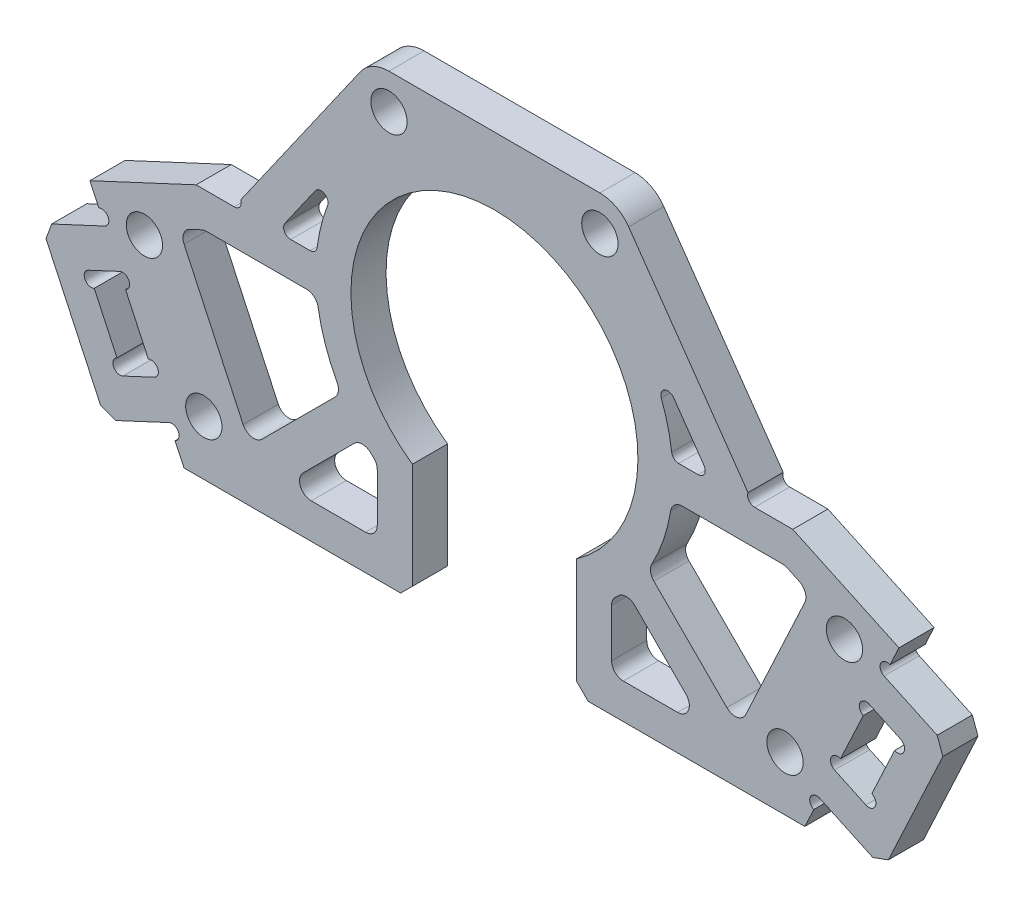
SolidWorks part; units mm, degrees
ref_plane "前视基准面" through (0, 0, 0) normal (0, 0, 1) x (1, 0, 0)
ref_plane "上视基准面" through (0, 0, 0) normal (0, 1, 0) x (1, 0, 0)
ref_plane "右视基准面" through (0, 0, 0) normal (1, 0, 0) x (0, 0, -1)
sketch "草图1" plane through (0, 0, 0) normal (0, 0, 1) x (1, 0, 0)
  line L0 (-34.5264, 8.6099) -> (-26.4967, -8.6099)
  line L1 (-29.455, -2.2658) -> (0, 11.4693) construction
  line L2 (0, -8.6099) -> (0, 8.6099) construction
  line L3 (-34.5264, 8.6099) -> (-25.4633, 12.8361)
  line L4 (-26.4967, -8.6099) -> (26.4967, -8.6099)
  line L5 (34.5264, 8.6099) -> (26.4967, -8.6099)
  line L6 (34.5264, 8.6099) -> (25.4633, 12.8361)
  line L7 (-25.4633, 12.8361) -> (25.4633, 12.8361)
  circle A0 centre (0, 11.4693) radius 9.5 construction
  circle A1 centre (0, 20.9693) radius 1.25 construction
  circle A2 centre (8.2272, 6.7193) radius 1.25 construction
  circle A3 centre (-8.2272, 6.7193) radius 1.25 construction
  circle A5 centre (0, 11.4693) radius 6.55 construction
  point P8 (0, 0)
  point P21 (-30.5115, 0)
  dimension "D4" = 19
  dimension "D5" = 2.5
  dimension "D8" = 10
  dimension "D9" = 13.1
  dimension "D1" = 32.5
  dimension "D2" = 25
  dimension "D3" = 19
  dimension "D7" = 2.5
  dimension "D6" = 3
extrude "凸台-拉伸1" add sketch "草图1" along normal mid plane 3
sketch "草图2" plane through (0, 0, 1.5) normal (0, 0, 1) x (1, 0, 0)
  line L0 (-33.2586, 5.891) -> (-38.6964, 3.3553)
  line L1 (-34.5264, 8.6099) -> (-26.4967, -8.6099) construction
  line L2 (-38.6964, 3.3553) -> (-33.2024, -8.4267)
  line L3 (-33.2024, -8.4267) -> (-27.7645, -5.891)
  line L4 (-27.7645, -5.891) -> (-29.0324, -3.1721)
  line L5 (-31.9907, 3.1721) -> (-34.6643, 1.9254)
  line L6 (-34.6643, 1.9254) -> (-31.706, -4.4188)
  line L7 (-31.706, -4.4188) -> (-29.0324, -3.1721)
  line L8 (-31.9907, 3.1721) -> (-33.2586, 5.891)
  line L9 (-30.5115, 0) -> (-33.1852, -1.2467) construction
  line L10 (0, 12.8361) -> (0, -8.6099) construction
  line L11 (-26.4967, -8.6099) -> (26.4967, -8.6099) construction
  line L12 (38.6964, 3.3553) -> (33.2024, -8.4267)
  line L13 (33.2586, 5.891) -> (38.6964, 3.3553)
  line L14 (31.9907, 3.1721) -> (33.2586, 5.891)
  line L15 (31.9907, 3.1721) -> (34.6643, 1.9254)
  line L16 (34.6643, 1.9254) -> (31.706, -4.4188)
  line L17 (31.706, -4.4188) -> (29.0324, -3.1721)
  line L18 (27.7645, -5.891) -> (29.0324, -3.1721)
  line L19 (33.2024, -8.4267) -> (27.7645, -5.891)
  line L20 (25.4633, 12.8361) -> (-25.4633, 12.8361) construction
  dimension "D1" = 13
  dimension "D2" = 6
  dimension "D3" = 2.95
  dimension "D4" = 7
extrude "凸台-拉伸2" add sketch "草图2" against normal blind 3
sketch "草图3" plane through (0, 0, 1.5) normal (0, 0, 1) x (1, 0, 0)
  line L0 (-34.5264, 8.6099) -> (-33.2586, 5.891) construction
  line L1 (-31.706, -4.4188) -> (-34.6643, 1.9254) construction
  line L2 (25.4633, 12.8361) -> (-25.4633, 12.8361) construction
  line L3 (-31.9907, 3.1721) -> (-29.0324, -3.1721) construction
  line L4 (-27.7645, -5.891) -> (-26.4967, -8.6099) construction
  line L5 (0, 12.8361) -> (0, -8.6099) construction
  line L6 (-26.4967, -8.6099) -> (26.4967, -8.6099) construction
  circle A0 centre (-33.5121, 6.4348) radius 0.6
  circle A1 centre (-34.4107, 1.3816) radius 0.6
  circle A2 centre (-31.9596, -3.875) radius 0.6
  circle A4 centre (-29.286, -2.6283) radius 0.6
  circle A5 centre (-31.7371, 2.6283) radius 0.6
  circle A6 centre (-27.511, -6.4348) radius 0.6
  circle A8 centre (27.511, -6.4348) radius 0.6
  circle A9 centre (31.7371, 2.6283) radius 0.6
  circle A10 centre (29.286, -2.6283) radius 0.6
  circle A11 centre (31.9596, -3.875) radius 0.6
  circle A12 centre (34.4107, 1.3816) radius 0.6
  circle A13 centre (33.5121, 6.4348) radius 0.6
  dimension "D1" = 1.2
extrude "切除-拉伸1" cut sketch "草图3" against normal through all
sketch "草图4" plane through (0, 0, 1.5) normal (0, 0, 1) x (1, 0, 0)
  line L0 (25.4633, 12.8361) -> (-25.4633, 12.8361) construction
  line L1 (-25.4633, 12.8361) -> (-34.5264, 8.6099) construction
  line L2 (-34.5264, 8.6099) -> (-33.7657, 6.9786) construction
  line L3 (-33.1852, -1.2467) -> (-30.5115, 0) construction
  line L4 (-32.2131, -3.3312) -> (-34.1572, 0.8378) construction
  line L5 (-31.4836, 2.0845) -> (-29.5395, -2.0845) construction
  line L6 (0, 12.8361) -> (0, -8.6099) construction
  line L7 (-26.4967, -8.6099) -> (26.4967, -8.6099) construction
  circle A0 centre (-29.8752, 6.917) radius 1.55
  circle A4 centre (-24.8038, -3.9587) radius 1.55
  circle A6 centre (24.8038, -3.9587) radius 1.55
  circle A7 centre (29.8752, 6.917) radius 1.55
  dimension "D1" = 3.5
  dimension "D2" = 3.5
  dimension "D3" = 3.1
extrude "切除-拉伸2" cut sketch "草图4" against normal through all
sketch "草图5" plane through (0, 0, 1.5) normal (0, 0, 1) x (1, 0, 0)
  line L0 (-24.7983, 9.8361) -> (-6.8472, 9.8361)
  line L1 (26.9144, 8.8493) -> (20.8466, -4.1632)
  line L2 (18.0506, -5.6099) -> (-18.0506, -5.6099)
  line L3 (-20.8466, -4.1632) -> (-26.9144, 8.8493)
  line L4 (-31.4836, 2.0845) -> (-29.5395, -2.0845) construction
  line L7 (29.5395, -2.0845) -> (31.4836, 2.0845) construction
  line L10 (25.4633, 12.8361) -> (-25.4633, 12.8361) construction
  line L13 (-26.4967, -8.6099) -> (26.4967, -8.6099) construction
  line L14 (-26.9144, 8.8493) -> (-24.7983, 9.8361)
  line L15 (-25.4633, 12.8361) -> (-34.5264, 8.6099) construction
  line L23 (0, -8.6099) -> (0, 12.8361) construction
  line L24 (26.9144, 8.8493) -> (24.7983, 9.8361)
  line L25 (-20.172, -5.6099) -> (-4.7259, 9.8361) construction
  line L26 (-18.0506, -5.6099) -> (-2.6046, 9.8361)
  line L27 (-20.8466, -4.1632) -> (-6.8472, 9.8361)
  line L28 (-19.1113, -6.6706) -> (-3.6653, 8.7754) construction
  line L29 (-2.6046, 9.8361) -> (2.6046, 9.8361)
  line L30 (-21.2326, -4.5493) -> (-5.7866, 10.8968) construction
  line L31 (18.0506, -5.6099) -> (2.6046, 9.8361)
  line L32 (20.8466, -4.1632) -> (6.8472, 9.8361)
  line L33 (6.8472, 9.8361) -> (24.7983, 9.8361)
  circle A5 centre (-29.8752, 6.917) radius 1.55 construction
  dimension "D1" = 3
  dimension "D4" = 45
  dimension "D5" = 3
  dimension "D6" = 1.5
  dimension "D2" = 3.5
  dimension "D3" = 3
  dimension "D7" = 1.5
extrude "切除-拉伸5" cut sketch "草图5" against normal through all
sketch "草图9" plane through (0, 0, 1.5) normal (0, 0, 1) x (1, 0, 0)
  circle A0 centre (0, 11.4693) radius 12.25
  dimension "D1" = 24.5
extrude "切除-拉伸6" cut sketch "草图9" against normal through all contours A0
sketch "草图10" plane through (0, 0, 1.5) normal (0, 0, 1) x (1, 0, 0)
  line L0 (-12.1735, 12.8361) -> (-15.1886, 12.8361)
  line L1 (-12.1735, 12.8361) -> (-25.4633, 12.8361) construction
  line L2 (12.1735, 12.8361) -> (15.1886, 12.8361)
  line L3 (25.4633, 12.8361) -> (12.1735, 12.8361) construction
  arc A0 (-12.1735, 12.8361) -> (12.1735, 12.8361) centre (0, 11.4693) ccw
  arc A1 (-15.1886, 12.8361) -> (15.1886, 12.8361) centre (0, 11.4693) ccw
  dimension "D1" = 3
extrude "凸台-拉伸4" add sketch "草图10" against normal blind 3
sketch "草图12" plane through (0, 0, -1.5) normal (0, 0, -1) x (-1, 0, 0)
  line L0 (0, 11.4693) -> (0, 61.4693) construction
  line L1 (-11.4575, 28.1901) -> (-22.2084, 12.8361)
  line L2 (-25.4633, 12.8361) -> (-12.1735, 12.8361) construction
  line L3 (-22.2084, 12.8361) -> (-12.1735, 12.8361)
  line L4 (-9, 29.4693) -> (9, 29.4693)
  line L5 (22.2084, 12.8361) -> (12.1735, 12.8361)
  line L6 (11.4575, 28.1901) -> (22.2084, 12.8361)
  circle A0 centre (-9, 26.4693) radius 1.55
  arc A1 (-9, 29.4693) -> (-11.4575, 28.1901) centre (-9, 26.4693) ccw
  arc A2 (12.1735, 12.8361) -> (-12.1735, 12.8361) centre (0, 11.4693) ccw
  arc A3 (9, 29.4693) -> (11.4575, 28.1901) centre (9, 26.4693) cw
  circle A4 centre (9, 26.4693) radius 1.55
  point P16 (0, 29.4693)
  dimension "D2" = 9
  dimension "D3" = 35
  dimension "D4" = 3.1
  dimension "D5" = 6
  dimension "D1" = 50
  dimension "D6" = 35
extrude "凸台-拉伸5" add sketch "草图12" against normal up to surface (3 mm away) up to face at (20.2262, 5.5715, 1.5)
sketch "草图13" plane through (0, 0, -1.5) normal (0, 0, -1) x (-1, 0, 0)
  line L0 (-7, 1.4163) -> (-7, -8.6099)
  line L1 (26.4967, -8.6099) -> (-26.4967, -8.6099) construction
  line L2 (-7, -8.6099) -> (7, -8.6099)
  line L3 (7, -8.6099) -> (7, 1.4163)
  line L4 (7, 1.4163) -> (-7, 1.4163)
  circle A0 centre (0, 11.4693) radius 12.25 construction
  dimension "D1" = 14
extrude "切除-拉伸7" cut sketch "草图13" against normal through all
sketch "草图14" plane through (0, 0, -1.5) normal (0, 0, -1) x (-1, 0, 0)
  line L0 (-7, 1.4163) -> (-7, -2.0792) construction
  line L1 (-7, -8.6099) -> (-10, -8.6099)
  line L2 (-7, -8.6099) -> (-7, 1.4163)
  line L3 (-7, 1.4163) -> (-10, 1.4163)
  line L4 (-10, -8.6099) -> (-10, 1.4163)
  line L5 (0, 0) -> (0, 23.7193) construction
  line L6 (7, 1.4163) -> (10, 1.4163)
  line L7 (10, -8.6099) -> (10, 1.4163)
  line L8 (7, -8.6099) -> (10, -8.6099)
  line L9 (7, -8.6099) -> (7, 1.4163)
  arc A0 (7, 1.4163) -> (-7, 1.4163) centre (0, 11.4693) ccw construction
  dimension "D1" = 3
extrude "凸台-拉伸6" add sketch "草图14" against normal up to surface (3 mm away) up to face at (20.2262, 5.5715, 1.5)
fillet "圆角1" radius 1 18 edges at (-26.9144, 8.8493, 0) (-24.7983, 9.8361, 0) (-15.1623, 9.8361, 0) (-13.0705, 3.6128, 0) (-20.8466, -4.1632, 0) (-10, -0.0443, 0) (-11.2581, 1.1826, 0) (-18.0506, -5.6099, 0) (-10, -5.6099, 0) (24.7983, 9.8361, 0) (26.9144, 8.8493, 0) (13.0705, 3.6128, 0) (15.1623, 9.8361, 0) (20.8466, -4.1632, 0) (11.2581, 1.1826, 0) (10, -5.6099, 0) (10, -0.0443, 0) (18.0506, -5.6099, 0)
chamfer "倒角1" distance 1 angle 45 6 edges at (33.2024, -8.4267, 0) (38.6964, 3.3553, 0) (-33.2024, -8.4267, 0) (-38.6964, 3.3553, 0) (-7, -8.6099, 0) (7, -8.6099, 0)
sketch "草图15" plane through (0, 0, 1.5) normal (0, 0, 1) x (1, 0, 0)
  line L0 (-22.2084, 12.8361) -> (-25.4633, 12.8361) construction
  line L1 (25.4633, 12.8361) -> (22.2084, 12.8361) construction
  circle A0 centre (-22.2084, 13.4361) radius 0.6
  circle A1 centre (22.2084, 13.4361) radius 0.6
  dimension "D1" = 1.2
extrude "切除-拉伸8" cut sketch "草图15" against normal through all
sketch "草图16" plane through (0, 0, 1.5) normal (0, 0, 1) x (1, 0, 0)
  line L1 (-18.5461, 12.8361) -> (-15.1886, 12.8361)
  line L2 (-9, 26.4693) -> (-19.1871, 11.9206)
  line L3 (-15.2934, 17.4814) -> (-18.5461, 12.8361)
  line L4 (-22.2084, 12.8361) -> (-25.4633, 12.8361) construction
  line L5 (0, 23.7193) -> (0, 11.4693) construction
  line L6 (18.5461, 12.8361) -> (15.1886, 12.8361)
  line L7 (15.2934, 17.4814) -> (18.5461, 12.8361)
  arc A0 (-14.2416, 16.9227) -> (-15.1886, 12.8361) centre (0, 11.4693) ccw
  arc A1 (7, 1.4163) -> (-7, 1.4163) centre (0, 11.4693) ccw construction
  arc A2 (-14.2416, 16.9227) -> (-15.2934, 17.4814) centre (-14.8019, 17.1372) ccw
  arc A3 (14.2416, 16.9227) -> (15.2934, 17.4814) centre (14.8019, 17.1372) cw
  arc A4 (14.2416, 16.9227) -> (15.1886, 12.8361) centre (0, 11.4693) cw
  dimension "D1" = 3
  dimension "D3" = 1.2
  dimension "D2" = 3
extrude "切除-拉伸9" cut sketch "草图16" against normal through all
fillet "圆角2" radius 0.6 4 edges at (15.1886, 12.8361, 0) (18.5461, 12.8361, 0) (-15.1886, 12.8361, 0) (-18.5461, 12.8361, 0)
